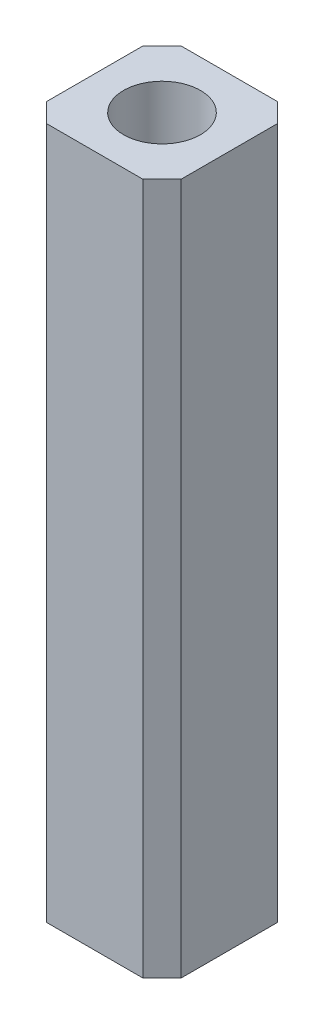
SolidWorks part; units mm, degrees
ref_plane "Front Plane" through (0, 0, 0) normal (0, 0, 1) x (1, 0, 0)
ref_plane "Top Plane" through (0, 0, 0) normal (0, 1, 0) x (1, 0, 0)
ref_plane "Right Plane" through (0, 0, 0) normal (1, 0, 0) x (0, 0, -1)
sketch "Sketch1" plane through (0, 0, 0) normal (0, 1, 0) x (1, 0, 0)
  line L0 (-1.75, 1) -> (1.75, 1) construction
  line L1 (-1.75, -1.75) -> (1.75, -1.75)
  line L2 (-1.75, -1.75) -> (-1.75, 1.75)
  line L3 (-1.75, 1.75) -> (1.75, 1.75)
  line L4 (1.75, -1.75) -> (1.75, 1.75)
  line L5 (-1.75, -1.75) -> (1.75, 1.75) construction
  line L6 (-1.75, 1.75) -> (1.75, -1.75) construction
  circle A0 centre (0, 0) radius 1
  dimension "D1" = 2
  dimension "D2" = 0.75
extrude "Boss-Extrude1" add sketch "Sketch1" along normal blind 18
chamfer "Chamfer1" distance 0.5 angle 45 4 edges at (1.75, 9, -1.75) (-1.75, 9, -1.75) (1.75, 9, 1.75) (-1.75, 9, 1.75)
